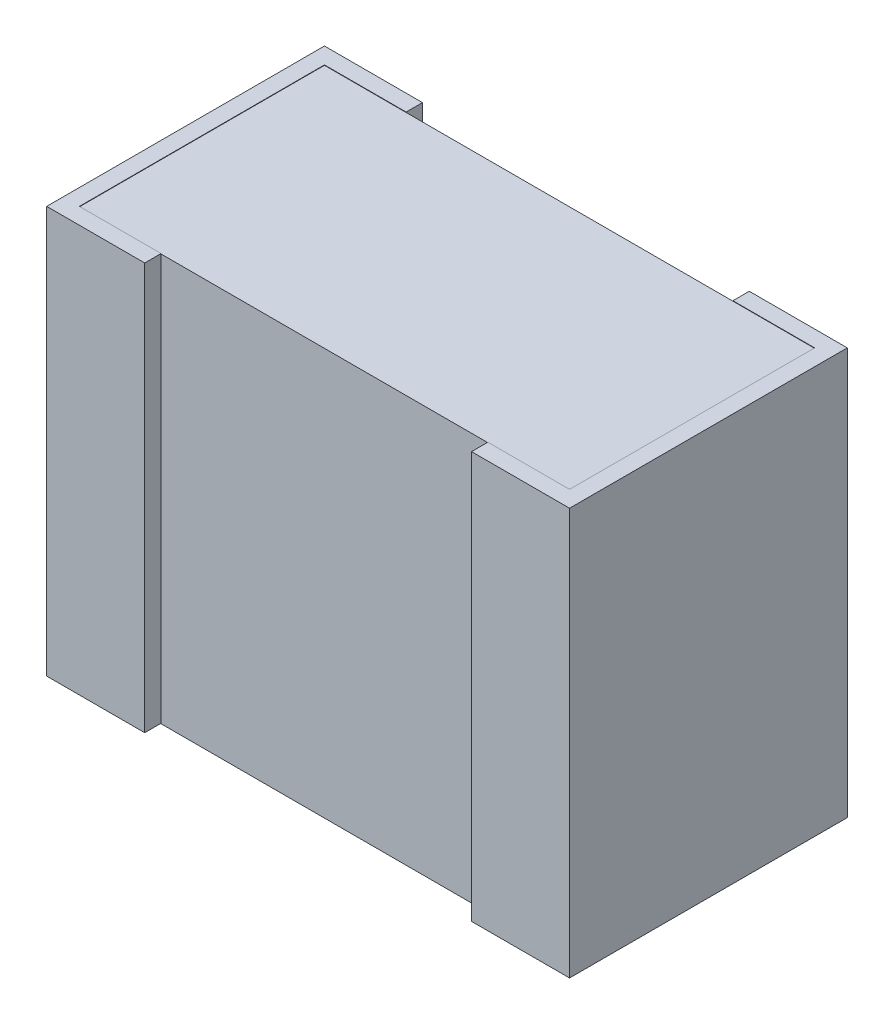
SolidWorks part; units mm, degrees
ref_plane "x/y" through (0, 0, 0) normal (0, 0, 1) x (1, 0, 0)
ref_plane "x/z" through (0, 0, 0) normal (0, 1, 0) x (1, 0, 0)
ref_plane "y/z" through (0, 0, 0) normal (1, 0, 0) x (0, 0, -1)
sketch "Sketch2" plane through (0, 0, 0) normal (0, 1, 0) x (1, 0, 0)
  line L0 (-1.5, -0.75) -> (1.5, -0.75)
  line L1 (-1.5, -0.75) -> (-1.5, 0.75)
  line L2 (1.5, 0.75) -> (-1.5, 0.75)
  line L3 (1.5, 0.75) -> (1.5, -0.75)
  dimension "D1" = 3
  dimension "D2" = 1.5
  dimension "D3" = 1.5
  dimension "D4" = 0.75
extrude "Base-Extrude" add sketch "Sketch2" along normal mid plane 2.49
ref_plane "Plane4" through (0, 1.2475, 0) normal (0, 1, 0) x (-1, 0, 0)
sketch "Sketch3" plane through (0, 1.2475, 0) normal (0, 1, 0) x (-1, 0, 0)
  line L0 (1, 0.85) -> (1, 0.75)
  line L1 (1.5, 0.75) -> (-1.5, 0.75) construction
  line L2 (1.6, 0.85) -> (1.6, -0.85)
  line L4 (1.6, 0.85) -> (1, 0.85)
  line L6 (1, -0.75) -> (1.5, -0.75)
  line L7 (1.5, -0.75) -> (1.5, 0.75)
  line L8 (1.5, 0.75) -> (1, 0.75)
  line L9 (1, -0.75) -> (1, -0.85)
  line L10 (1, -0.85) -> (1.6, -0.85)
  dimension "D1" = 0.1
  dimension "D2" = 0.1
  dimension "D3" = 0.1
  dimension "D4" = 0.5
  dimension "D5" = 0.5
extrude "Boss-Extrude8" add sketch "Sketch3" against normal blind 2.49
mirror "Espelhar1" about plane through (0, 0, 0) normal (1, 0, 0) of "Boss-Extrude8"
